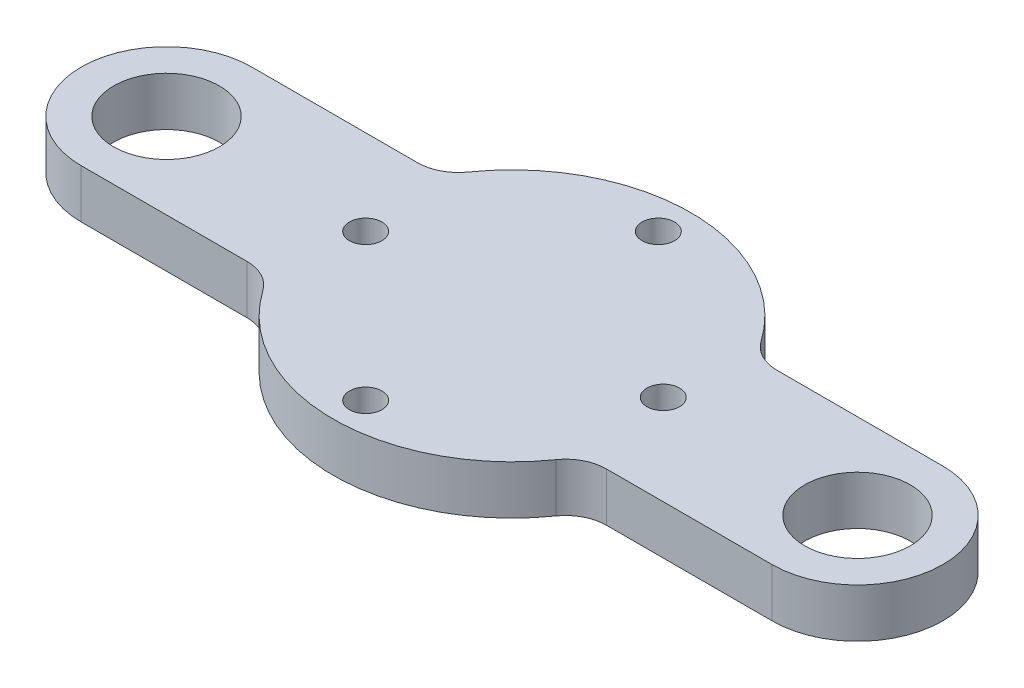
SolidWorks part; units mm, degrees
material "6061 Alloy"
ref_plane "Front Plane" through (0, 0, 0) normal (0, 0, 1) x (1, 0, 0)
ref_plane "Top Plane" through (0, 0, 0) normal (0, 1, 0) x (1, 0, 0)
ref_plane "Right Plane" through (0, 0, 0) normal (1, 0, 0) x (0, 0, -1)
sketch "Sketch1" plane through (0, 0, 0) normal (0, 1, 0) x (1, 0, 0)
  line L0 (0, 0) -> (0, 10.5)
  line L1 (0, 0) -> (0, -10.5)
  line L2 (0, 0) -> (-42.5, 0)
  line L3 (0, 0) -> (42.5, 0)
  line L4 (-42.5, 10.5) -> (42.5, 10.5)
  line L5 (-42.5, -10.5) -> (42.5, -10.5)
  line L6 (-42.5, 0) -> (-53, 0)
  circle A0 centre (0, 0) radius 22
  circle A1 centre (-42.5, 0) radius 10.5
  circle A2 centre (42.5, 0) radius 10.5
  circle A3 centre (-42.5, 0) radius 6.5
  circle A4 centre (42.5, 0) radius 6.5
  circle A5 centre (0, 0) radius 18
  circle A6 centre (17.9894, 0.6177) radius 2
  circle A7 centre (0, 18) radius 2
  circle A8 centre (-18, 0) radius 2
  circle A9 centre (0, -18) radius 2
  circle A10 centre (-22.1077, 15.5) radius 5
  circle A11 centre (22.1077, 15.5) radius 5
  circle A12 centre (22.1077, -15.5) radius 5
  circle A13 centre (-22.1077, -15.5) radius 5
  dimension "D1" = 44
  dimension "D6" = 21
  dimension "D7" = 21
  dimension "D2" = 10.5
  dimension "D3" = 10.5
  dimension "D4" = 42.5
  dimension "D5" = 42.5
extrude "Boss-Extrude1" add sketch "Sketch1" along normal blind 6
